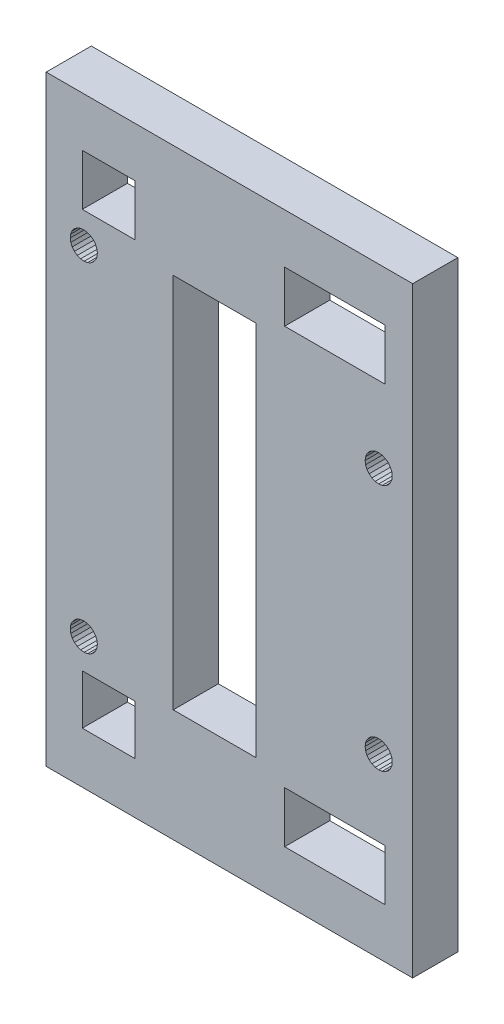
SolidWorks part; units mm, degrees
material "Maple"
ref_plane "Front Plane" through (0, 0, 0) normal (0, 0, 1) x (1, 0, 0)
ref_plane "Top Plane" through (0, 0, 0) normal (0, 1, 0) x (1, 0, 0)
ref_plane "Right Plane" through (0, 0, 0) normal (1, 0, 0) x (0, 0, -1)
sketch "Sketch1" plane through (0, 0, 0) normal (0, 0, 1) x (1, 0, 0)
  line L1450 (-306.5477, -310.3318) -> (-306.7275, -310.7659)
  line L1451 (-306.4863, -309.8659) -> (-306.5477, -310.3318)
  line L1452 (-306.5477, -309.4001) -> (-306.4863, -309.8659)
  line L1453 (-306.7275, -308.9659) -> (-306.5477, -309.4001)
  line L1454 (-307.0136, -308.5931) -> (-306.7275, -308.9659)
  line L1455 (-307.3863, -308.3071) -> (-307.0136, -308.5931)
  line L1456 (-307.4689, -352.8659) -> (-307.4689, -359.6659)
  line L1457 (-340.6689, -359.4659) -> (-347.6689, -359.4659)
  line L1458 (-340.6689, -352.8659) -> (-340.6689, -359.4659)
  line L1459 (-347.6689, -352.8659) -> (-340.6689, -352.8659)
  line L1460 (-320.7812, -352.8659) -> (-307.4689, -352.8659)
  line L1461 (-320.7812, -359.6659) -> (-320.7812, -352.8659)
  line L1462 (-307.4689, -359.6659) -> (-320.7812, -359.6659)
  line L1463 (-307.4689, -299.7659) -> (-307.4689, -292.9659)
  line L1464 (-349.0055, -349.7534) -> (-349.1958, -349.3237)
  line L1465 (-348.7105, -350.1191) -> (-349.0055, -349.7534)
  line L1466 (-348.3309, -350.3961) -> (-348.7105, -350.1191)
  line L1467 (-346.9611, -350.5428) -> (-347.4254, -350.6154)
  line L1468 (-309.1863, -311.4248) -> (-309.5591, -311.1387)
  line L1469 (-308.7522, -311.6046) -> (-309.1863, -311.4248)
  line L1470 (-308.2863, -311.6659) -> (-308.7522, -311.6046)
  line L1471 (-307.8205, -311.6046) -> (-308.2863, -311.6659)
  line L1472 (-307.3863, -311.4248) -> (-307.8205, -311.6046)
  line L1473 (-307.0136, -311.1387) -> (-307.3863, -311.4248)
  line L1474 (-306.7275, -310.7659) -> (-307.0136, -311.1387)
  line L1475 (-307.0136, -341.4931) -> (-306.7275, -341.8659)
  line L1476 (-307.3863, -341.2071) -> (-307.0136, -341.4931)
  line L1477 (-307.8205, -341.0273) -> (-307.3863, -341.2071)
  line L1478 (-307.8205, -308.1273) -> (-307.3863, -308.3071)
  line L1479 (-308.2863, -308.0659) -> (-307.8205, -308.1273)
  line L1480 (-308.7522, -308.1273) -> (-308.2863, -308.0659)
  line L1481 (-309.1863, -308.3071) -> (-308.7522, -308.1273)
  line L1482 (-309.5591, -308.5931) -> (-309.1863, -308.3071)
  line L1483 (-309.8452, -308.9659) -> (-309.5591, -308.5931)
  line L1484 (-310.025, -309.4001) -> (-309.8452, -308.9659)
  line L1485 (-310.0863, -309.8659) -> (-310.025, -309.4001)
  line L1486 (-310.025, -310.3318) -> (-310.0863, -309.8659)
  line L1487 (-347.0425, -302.0672) -> (-346.6044, -302.2371)
  line L1488 (-307.4689, -292.9659) -> (-320.7812, -292.9659)
  line L1489 (-320.7812, -292.9659) -> (-320.7812, -299.7659)
  line L1490 (-320.7812, -299.7659) -> (-307.4689, -299.7659)
  line L1491 (-340.6689, -299.7659) -> (-340.6689, -292.9659)
  line L1492 (-340.6689, -292.9659) -> (-347.6689, -292.9659)
  line L1493 (-347.6689, -292.9659) -> (-347.6689, -299.7659)
  line L1494 (-346.2272, -347.5127) -> (-345.9323, -347.8785)
  line L1495 (-346.6068, -347.2358) -> (-346.2272, -347.5127)
  line L1496 (-347.5096, -302.0164) -> (-347.0425, -302.0672)
  line L1497 (-347.974, -302.0883) -> (-347.5096, -302.0164)
  line L1498 (-348.4039, -302.2779) -> (-347.974, -302.0883)
  line L1499 (-348.7702, -302.5723) -> (-348.4039, -302.2779)
  line L1500 (-349.0477, -302.9514) -> (-348.7702, -302.5723)
  line L1501 (-347.0452, -347.0665) -> (-346.6068, -347.2358)
  line L1502 (-347.5124, -347.0165) -> (-347.0452, -347.0665)
  line L1503 (-347.9767, -347.089) -> (-347.5124, -347.0165)
  line L1504 (-348.4063, -347.2793) -> (-347.9767, -347.089)
  line L1505 (-348.7721, -347.5743) -> (-348.4063, -347.2793)
  line L1506 (-349.049, -347.9539) -> (-348.7721, -347.5743)
  line L1507 (-349.2183, -348.3922) -> (-349.049, -347.9539)
  line L1508 (-306.5477, -343.2318) -> (-306.7275, -343.6659)
  line L1509 (-309.8452, -310.7659) -> (-310.025, -310.3318)
  line L1510 (-309.5591, -311.1387) -> (-309.8452, -310.7659)
  line L1511 (-349.007, -304.751) -> (-349.1966, -304.321)
  line L1512 (-348.7125, -305.1172) -> (-349.007, -304.751)
  line L1513 (-348.3334, -305.3948) -> (-348.7125, -305.1172)
  line L1514 (-347.8953, -305.5647) -> (-348.3334, -305.3948)
  line L1515 (-347.4282, -305.6155) -> (-347.8953, -305.5647)
  line L1516 (-345.8901, -304.6804) -> (-346.1676, -305.0596)
  line L1517 (-345.7201, -304.2424) -> (-345.8901, -304.6804)
  line L1518 (-345.6693, -303.7752) -> (-345.7201, -304.2424)
  line L1519 (-345.7412, -303.3108) -> (-345.6693, -303.7752)
  line L1520 (-345.9308, -302.8809) -> (-345.7412, -303.3108)
  line L1521 (-346.2252, -302.5147) -> (-345.9308, -302.8809)
  line L1522 (-349.2684, -348.8595) -> (-349.2183, -348.3922)
  line L1523 (-346.5315, -350.3526) -> (-346.9611, -350.5428)
  line L1524 (-346.1657, -350.0576) -> (-346.5315, -350.3526)
  line L1525 (-345.8887, -349.678) -> (-346.1657, -350.0576)
  line L1526 (-345.7195, -349.2396) -> (-345.8887, -349.678)
  line L1527 (-345.6694, -348.7724) -> (-345.7195, -349.2396)
  line L1528 (-345.742, -348.3082) -> (-345.6694, -348.7724)
  line L1529 (-306.4863, -342.7659) -> (-306.5477, -343.2318)
  line L1530 (-306.5477, -342.3001) -> (-306.4863, -342.7659)
  line L1531 (-306.7275, -341.8659) -> (-306.5477, -342.3001)
  line L1532 (-303.7706, -366.2659) -> (-303.7706, -286.3659)
  line L1533 (-352.4689, -366.2659) -> (-303.7706, -366.2659)
  line L1534 (-352.4689, -286.3659) -> (-352.4689, -366.2659)
  line L1535 (-335.5863, -351.3159) -> (-324.5864, -351.3159)
  line L1536 (-324.5864, -351.3159) -> (-324.5864, -301.316)
  line L1537 (-324.5864, -301.316) -> (-335.5863, -301.316)
  line L1538 (-335.5863, -301.316) -> (-335.5863, -351.3159)
  line L1539 (-347.6689, -359.4659) -> (-347.6689, -352.8659)
  line L1540 (-308.2863, -340.9659) -> (-307.8205, -341.0273)
  line L1541 (-308.7522, -341.0273) -> (-308.2863, -340.9659)
  line L1542 (-309.1863, -341.2071) -> (-308.7522, -341.0273)
  line L1543 (-309.5591, -341.4931) -> (-309.1863, -341.2071)
  line L1544 (-309.8452, -341.8659) -> (-309.5591, -341.4931)
  line L1545 (-310.025, -342.3001) -> (-309.8452, -341.8659)
  line L1546 (-310.0863, -342.7659) -> (-310.025, -342.3001)
  line L1547 (-310.025, -343.2318) -> (-310.0863, -342.7659)
  line L1548 (-309.8452, -343.6659) -> (-310.025, -343.2318)
  line L1549 (-309.5591, -344.0387) -> (-309.8452, -343.6659)
  line L1550 (-309.1863, -344.3248) -> (-309.5591, -344.0387)
  line L1551 (-308.7522, -344.5046) -> (-309.1863, -344.3248)
  line L1552 (-308.2863, -344.5659) -> (-308.7522, -344.5046)
  line L1553 (-307.8205, -344.5046) -> (-308.2863, -344.5659)
  line L1554 (-307.3863, -344.3248) -> (-307.8205, -344.5046)
  line L1555 (-303.7706, -286.3659) -> (-352.4689, -286.3659)
  line L1556 (-347.6689, -299.7659) -> (-340.6689, -299.7659)
  line L1557 (-345.9323, -347.8785) -> (-345.742, -348.3082)
  line L1558 (-347.4254, -350.6154) -> (-347.8926, -350.5654)
  line L1559 (-347.8926, -350.5654) -> (-348.3309, -350.3961)
  line L1560 (-349.1958, -349.3237) -> (-349.2684, -348.8595)
  line L1561 (-306.7275, -343.6659) -> (-307.0136, -344.0387)
  line L1562 (-307.0136, -344.0387) -> (-307.3863, -344.3248)
  line L1563 (-346.6044, -302.2371) -> (-346.2252, -302.5147)
  line L1564 (-346.1676, -305.0596) -> (-346.5338, -305.354)
  line L1565 (-346.5338, -305.354) -> (-346.9638, -305.5436)
  line L1566 (-346.9638, -305.5436) -> (-347.4282, -305.6155)
  line L1567 (-349.1966, -304.321) -> (-349.2684, -303.8567)
  line L1568 (-349.2684, -303.8567) -> (-349.2176, -303.3895)
  line L1569 (-349.2176, -303.3895) -> (-349.0477, -302.9514)
  line L8524 (-307.8055, -325.9226) -> (-307.8092, -325.9506)
  line L8525 (-307.8092, -325.8945) -> (-307.8055, -325.9226)
  line L8865 (-331.6618, -355.9377) -> (-330.6003, -360.2456)
  line L8866 (-330.6003, -360.2456) -> (-329.67, -355.9377)
  line L8867 (-329.67, -355.9377) -> (-330.6003, -360.2456)
  line L8868 (-330.6003, -360.2456) -> (-331.6618, -355.9377)
  line L8869 (-330.388, -355.9377) -> (-329.3266, -360.2456)
  line L8870 (-329.3266, -360.2456) -> (-328.3962, -355.9377)
  line L8871 (-328.3962, -355.9377) -> (-329.3266, -360.2456)
  line L8872 (-329.3266, -360.2456) -> (-330.388, -355.9377)
extrude "Boss-Extrude1" add sketch "Sketch1" along normal blind 6
